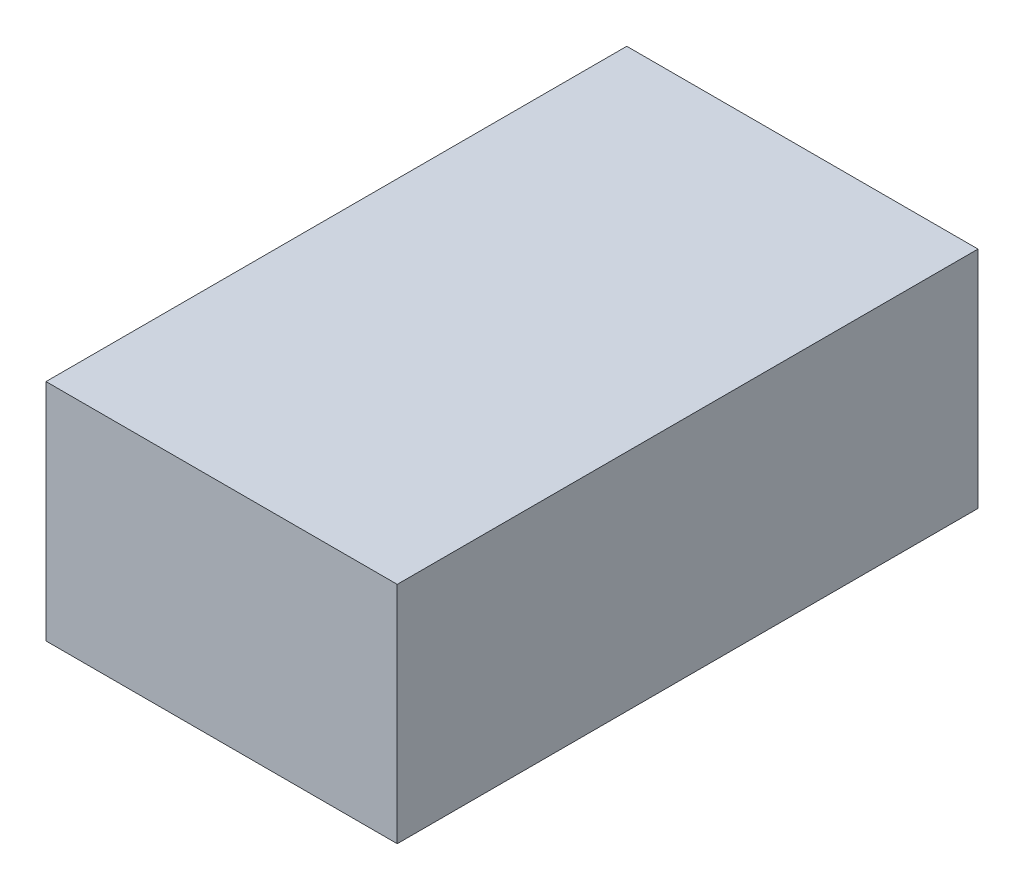
SolidWorks part; units mm, degrees
ref_plane "Front Plane" through (0, 0, 0) normal (0, 0, 1) x (1, 0, 0)
ref_plane "Top Plane" through (0, 0, 0) normal (0, 1, 0) x (1, 0, 0)
ref_plane "Right Plane" through (0, 0, 0) normal (1, 0, 0) x (0, 0, -1)
ref_plane "Plane1" through (0, 0, 30) normal (0, 0, 1) x (1, 0, 0)
sketch "Sketch1" plane through (0, 0, 30) normal (0, 0, 1) x (1, 0, 0)
  line L0 (160.2679, -105) -> (-160.2679, -105)
  line L5 (160.2679, -105) -> (160.2679, 100.0066)
  line L6 (-160.2679, -105) -> (-160.2679, 100.0066)
  line L7 (160.2679, 100.0066) -> (-160.2679, 100.0066)
  dimension "D1" = 100.0066
extrude "Boss-Extrude1" add sketch "Sketch1" against normal blind 530
sketch "Sketch2" plane through (0, -105, 0) normal (0, -1, 0) x (1, 0, 0)
  line L1 (-130.2679, 0) -> (130.2721, 0)
  line L2 (-130.2679, 0) -> (-130.2679, -470)
  line L3 (-130.2679, -470) -> (130.2721, -470)
  line L4 (130.2721, 0) -> (130.2721, -470)
extrude "Cut-Extrude1" cut sketch "Sketch2" against normal blind 30
